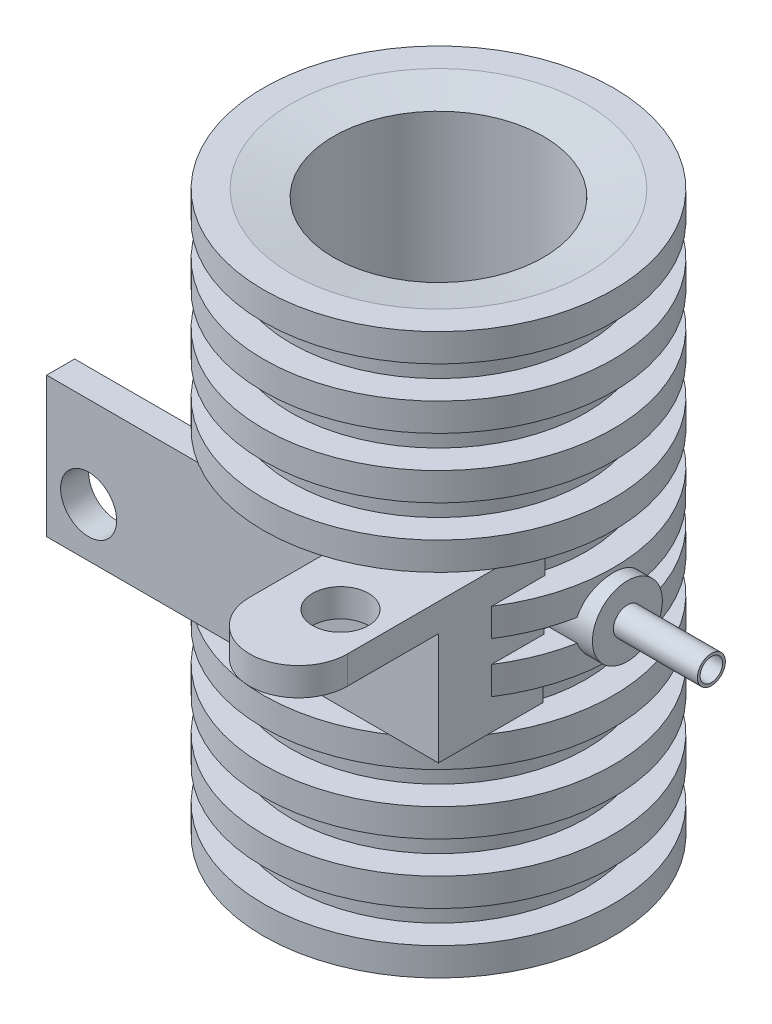
SolidWorks part; units mm, degrees
ref_plane "Alzado" through (0, 0, 0) normal (0, 0, 1) x (1, 0, 0)
ref_plane "Planta" through (0, 0, 0) normal (0, 1, 0) x (1, 0, 0)
ref_plane "Vista lateral" through (0, 0, 0) normal (1, 0, 0) x (0, 0, -1)
sketch "Croquis1" plane through (0, 0, 0) normal (0, 0, 1) x (1, 0, 0)
  line L0 (0, 0.5) -> (0, 39.5) construction
  line L1 (-10.5295, 40) -> (-12.5, 40) construction
  line L2 (-10.5295, 40) -> (-12.5, 40)
  line L3 (0, 20) -> (-21.7347, 20) construction
  line L4 (-12.5, 40) -> (-12.5, 38)
  line L5 (-12.5, 38) -> (-10.5295, 38)
  line L6 (-10.5295, 38) -> (-10.5295, 35.7)
  line L7 (-10.5295, 35.7) -> (-12.5, 35.7)
  line L8 (-12.5, 35.7) -> (-12.5, 33.7)
  line L9 (-12.5, 33.7) -> (-10.5295, 33.7)
  line L10 (-10.5295, 33.7) -> (-10.5295, 31.4)
  line L11 (-10.5295, 31.4) -> (-12.5, 31.4)
  line L12 (-12.5, 31.4) -> (-12.5, 29.4)
  line L13 (-12.5, 29.4) -> (-10.5295, 29.4)
  line L14 (-10.5295, 29.4) -> (-10.5295, 27.1)
  line L15 (-10.5295, 27.1) -> (-12.5, 27.1)
  line L16 (-12.5, 27.1) -> (-12.5, 25.1)
  line L17 (-12.5, 25.1) -> (-10.5295, 25.1)
  line L18 (-10.5295, 25.1) -> (-10.5295, 22.8)
  line L19 (-10.5295, 22.8) -> (-12.5, 22.8)
  line L20 (-12.5, 22.8) -> (-12.5, 20.8)
  line L21 (-12.5, 20.8) -> (-10.5295, 20.8)
  line L22 (-10.5295, 20.8) -> (-10.5295, 19.2)
  line L23 (-10.5295, 19.2) -> (-12.5, 19.2)
  line L24 (-12.5, 19.2) -> (-12.5, 17.2)
  line L25 (-12.5, 17.2) -> (-10.5295, 17.2)
  line L26 (-10.5295, 17.2) -> (-10.5295, 14.9)
  line L27 (-10.5295, 14.9) -> (-12.5, 14.9)
  line L28 (-12.5, 14.9) -> (-12.5, 12.9)
  line L29 (-12.5, 12.9) -> (-10.5295, 12.9)
  line L30 (-10.5295, 12.9) -> (-10.5295, 10.6)
  line L31 (-10.5295, 10.6) -> (-12.5, 10.6)
  line L32 (-12.5, 10.6) -> (-12.5, 8.6)
  line L33 (-12.5, 8.6) -> (-10.5295, 8.6)
  line L34 (-10.5295, 8.6) -> (-10.5295, 6.3)
  line L35 (-10.5295, 6.3) -> (-12.5, 6.3)
  line L36 (-12.5, 6.3) -> (-12.5, 4.3)
  line L37 (-12.5, 4.3) -> (-10.5295, 4.3)
  line L38 (-10.5295, 4.3) -> (-10.5295, 2)
  line L39 (-10.5295, 2) -> (-12.5, 2)
  line L40 (-12.5, 2) -> (-12.5, 0)
  line L41 (-12.5, 0) -> (-10.5295, 0)
  line L42 (0, 0.5) -> (0, 39.5)
  line L43 (-10.5295, 40) -> (-7.5, 39.5)
  line L44 (-7.5, 39.5) -> (0, 39.5)
  line L45 (-10.5295, 0) -> (-7.5, 0.5)
  line L46 (-7.5, 0.5) -> (0, 0.5)
  dimension "D3" = 2
  dimension "D4" = 2.3
  dimension "D5" = 2
  dimension "D6" = 2
  dimension "D7" = 2
  dimension "D8" = 2.3
  dimension "D9" = 2.3
  dimension "D10" = 2.3
  dimension "D11" = 2
  dimension "D12" = 2
  dimension "D13" = 2
  dimension "D14" = 2
  dimension "D15" = 2
  dimension "D16" = 2
  dimension "D17" = 2.3
  dimension "D18" = 2.3
  dimension "D19" = 2.3
  dimension "D20" = 2.3
  dimension "D22" = 7.5
  dimension "D24" = 7.5
revolve "Revolución2" add sketch "Croquis1" angle 360 about L0
sketch "Croquis2" plane through (0, 39.5, 0) normal (0, 1, 0) x (1, 0, 0)
  circle A0 centre (0, 0) radius 7.5
extrude "Cortar-Extruir1" cut sketch "Croquis2" against normal blind 100
ref_plane "Plano1" through (0, 0, 10.5295) normal (0, 0, 1) x (1, 0, 0)
sketch "Croquis3" plane through (0, 0, 10.5295) normal (0, 0, 1) x (1, 0, 0)
  line L0 (0, 40) -> (0, 0) construction
  line L1 (12.5, 40) -> (-12.5, 40) construction
  line L2 (-10.5295, 20) -> (10.5295, 20) construction
  line L3 (-10.5295, 20.8) -> (-10.5295, 19.2) construction
  line L4 (10.5295, 19.2) -> (10.5295, 20.8) construction
  line L5 (-10.5295, 25) -> (-17.4705, 25)
  line L6 (10.5295, 25) -> (-10.5295, 25)
  line L7 (10.5295, 25) -> (10.5295, 15)
  line L8 (10.5295, 15) -> (-10.5295, 15)
  line L9 (-10.5295, 25) -> (-10.5295, 15)
  line L10 (10.5295, 25) -> (-10.5295, 15) construction
  line L11 (10.5295, 15) -> (-10.5295, 25) construction
  line L12 (-17.4705, 25) -> (-17.4705, 15)
  line L13 (-17.4705, 15) -> (-10.5295, 15)
  point P11 (0, 20)
  dimension "D1" = 10
  dimension "D2" = 28
extrude "Saliente-Extruir1" add sketch "Croquis3" against normal blind 2 contours L12 L13 L9 L5 | L6 L9 L8 L7
sketch "Croquis4" plane through (0, 0, 10.5295) normal (0, 0, 1) x (1, 0, 0)
  line L0 (-17.4705, 25) -> (-17.4705, 15)
  line L1 (-17.4705, 15) -> (10.5295, 15)
  line L2 (10.5295, 15) -> (10.5295, 25)
  line L3 (10.5295, 25) -> (-17.4705, 25)
extrude "Cortar-Extruir2" cut sketch "Croquis4" along normal blind 2
sketch "Croquis5" plane through (10.5295, 0, 0) normal (1, 0, 0) x (0, 0, -1)
  line L0 (-8.5295, 25) -> (-2.8893, 25)
  line L1 (-2.8893, 25) -> (-3.0685, 15)
  line L2 (-3.0685, 15) -> (-8.4113, 15)
  line L3 (-8.4113, 15) -> (-8.5295, 15)
  line L4 (-8.5295, 25) -> (-8.5295, 15)
extrude "Saliente-Extruir2" add sketch "Croquis5" against normal blind 2
sketch "Croquis7" plane through (0, 25, 0) normal (0, 1, 0) x (1, 0, 0)
  line L0 (10.5295, -10.5295) -> (10.5295, -17.0295)
  line L2 (3.5295, -17.0295) -> (3.5295, -10.5295)
  line L3 (10.5295, -10.5295) -> (0, -10.5295) construction
  line L4 (3.5295, -10.5295) -> (10.5295, -10.5295)
  arc A0 (3.5295, -17.0295) -> (10.5295, -17.0295) centre (7.0295, -17.0295) ccw
extrude "Saliente-Extruir3" add sketch "Croquis7" against normal blind 2
sketch "Croquis8" plane through (0, 0, 0) normal (1, 0, 0) x (0, 0, -1)
  line L0 (0, 40) -> (0, 0) construction
  line L1 (12.5, 40) -> (-12.5, 40) construction
  circle A0 centre (0, 20) radius 2.5
  dimension "D1" = 5
extrude "Saliente-Extruir4" add sketch "Croquis8" along normal blind 19.5
sketch "Croquis9" plane through (19.5, 0, 0) normal (1, 0, 0) x (0, 0, -1)
  circle A0 centre (0, 20) radius 1
  circle A1 centre (0, 20) radius 2.5
  dimension "D1" = 2
extrude "Cortar-Extruir3" cut sketch "Croquis9" against normal blind 6
sketch "Croquis10" plane through (19.5, 0, 0) normal (1, 0, 0) x (0, 0, -1)
  circle A0 centre (0, 20) radius 0.804
extrude "Cortar-Extruir4" cut sketch "Croquis10" against normal blind 16
sketch "Croquis11" plane through (0, 40, 0) normal (0, 1, 0) x (1, 0, 0)
  circle A0 centre (0, 0) radius 7.5
extrude "Cortar-Extruir5" cut sketch "Croquis11" against normal blind 86
sketch "Croquis12" plane through (0, 0, 10.5295) normal (0, 0, 1) x (1, 0, 0)
  line L0 (-17.4705, 22) -> (-2.2255, 22)
  line L1 (-17.4705, 25) -> (-17.4705, 15) construction
  line L2 (-17.4705, 15) -> (0, 15) construction
  line L3 (-17.4705, 22) -> (-17.4705, 15) construction
  line L4 (-17.4705, 18.5) -> (-16.4705, 18.5) construction
  line L5 (-17.4705, 16.5) -> (-10.7806, 16.5) construction
  circle A0 centre (-14.4705, 18.5) radius 2
  point P12 (-16.4705, 18.5)
  dimension "D2" = 4
  dimension "D1" = 7
  dimension "D3" = 1
  dimension "D4" = 2
extrude "Cortar-Extruir7" cut sketch "Croquis12" against normal blind 86 contours A0
sketch "Croquis14" plane through (0, 23, 0) normal (0, -1, 0) x (1, 0, 0)
  line L0 (10.5295, 10.5295) -> (3.5295, 10.5295) construction
  line L1 (10.5295, 17.0295) -> (10.5295, 10.5295) construction
  circle A0 centre (7.5295, 14.5295) radius 2
  point P2 (7.5295, 12.5295)
  point P3 (9.5295, 14.5295)
  dimension "D3" = 4
  dimension "D1" = 2
  dimension "D2" = 1
extrude "Cortar-Extruir8" cut sketch "Croquis14" against normal blind 86
ref_plane "Plano2" through (0, 20, 0) normal (0, -1, 0) x (-1, 0, 0)
sketch "Croquis15" plane through (0, 20, 0) normal (0, -1, 0) x (-1, 0, 0)
  line L0 (-6.8355, -3.0864) -> (-6.8355, 3.0864)
  arc A0 (-6.8355, 3.0864) -> (-6.8355, -3.0864) centre (0, 0) ccw
extrude "Saliente-Extruir5" add sketch "Croquis15" against normal blind 1
scale "Escala1" scale about centroid uniform scaling yes scale factor 7
